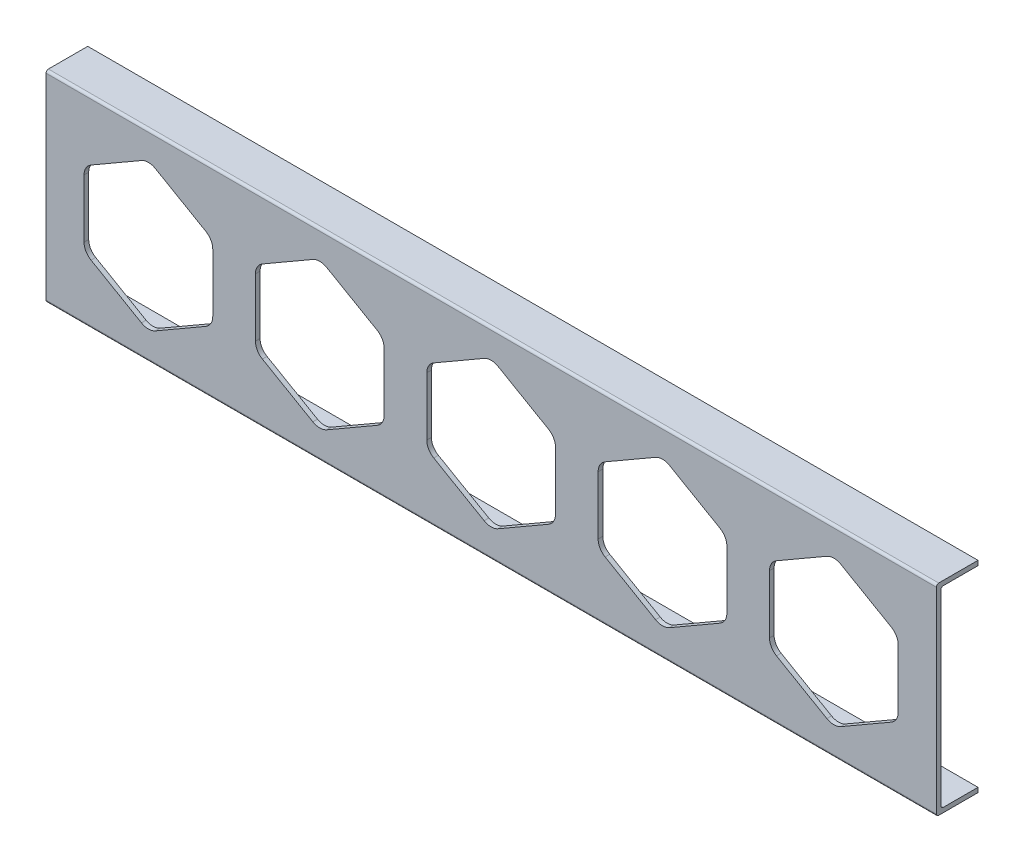
SolidWorks part; units mm, degrees
material "6061-T6 (SS)"
ref_plane "Front" through (0, 0, 0) normal (0, 0, 1) x (1, 0, 0)
ref_plane "Top" through (0, 0, 0) normal (0, 1, 0) x (1, 0, 0)
ref_plane "Right" through (0, 0, 0) normal (1, 0, 0) x (0, 0, -1)
sketch "Sketch1" plane through (0, 0, 0) normal (1, 0, 0) x (0, 0, -1)
  line L0 (-0.762, 67.2998) -> (12.7, 67.2998)
  line L1 (0.8255, 0) -> (12.7, 0)
  line L2 (0, 0.8255) -> (0, 64.8868)
  line L3 (0.8255, 65.7123) -> (12.7, 65.7123)
  line L5 (-1.5875, -0.762) -> (-1.5875, 66.4743)
  line L6 (-0.762, -1.5875) -> (12.7, -1.5875)
  line L7 (12.7, 65.7123) -> (12.7, 67.2998)
  line L8 (12.7, 0) -> (12.7, -1.5875)
  line L9 (-1.5875, -1.5875) -> (-1.5875, 67.2998) construction
  line L10 (-1.5875, -1.5875) -> (12.7, -1.5875) construction
  line L11 (0, 0) -> (12.7, 0) construction
  line L12 (0, 0) -> (0, 65.7123) construction
  line L13 (-1.5875, 67.2998) -> (12.7, 67.2998) construction
  line L14 (0, 65.7123) -> (12.7, 65.7123) construction
  arc A0 (-1.5875, -0.762) -> (-0.762, -1.5875) centre (-0.762, -0.762) ccw
  arc A1 (0.8255, 0) -> (0, 0.8255) centre (0.8255, 0.8255) cw
  arc A2 (-0.762, 67.2998) -> (-1.5875, 66.4743) centre (-0.762, 66.4743) ccw
  arc A3 (0, 64.8868) -> (0.8255, 65.7123) centre (0.8255, 64.8868) cw
  point P15 (0, 0)
  dimension "D4" = 0.8255
  dimension "D2" = 12.7
  dimension "D3" = 1.5875
extrude "Boss-Extrude1" add sketch "Sketch1" along normal blind 304.8
sketch "Sketch2" plane through (0, 0, 1.5875) normal (0, 0, 1) x (1, 0, 0)
  line L0 (35.0626, 32.8562) -> (35.0626, 66.4743) construction
  line L1 (32.6813, 56.9215) -> (15.412, 46.9511)
  line L2 (13.0307, 42.8266) -> (13.0307, 22.8857)
  line L3 (15.412, 18.7613) -> (32.6813, 8.7908)
  line L4 (37.4438, 8.7908) -> (54.7132, 18.7613)
  line L5 (57.0944, 22.8857) -> (57.0944, 42.8266)
  line L6 (54.7132, 46.9511) -> (37.4438, 56.9215)
  line L7 (304.8, 66.4743) -> (0, 66.4743) construction
  line L8 (35.0626, 32.8562) -> (35.0626, -0.762) construction
  line L9 (304.8, -0.762) -> (0, -0.762) construction
  line L10 (91.35, 56.9215) -> (74.0807, 46.9511)
  line L11 (71.6994, 42.8266) -> (71.6994, 22.8857)
  line L12 (74.0807, 18.7613) -> (91.35, 8.7908)
  line L13 (96.1125, 8.7908) -> (113.3819, 18.7613)
  line L14 (115.7631, 22.8857) -> (115.7631, 42.8266)
  line L15 (113.3819, 46.9511) -> (96.1125, 56.9215)
  line L16 (150.0188, 56.9215) -> (132.7494, 46.9511)
  line L17 (130.3681, 42.8266) -> (130.3681, 22.8857)
  line L18 (132.7494, 18.7613) -> (150.0188, 8.7908)
  line L19 (154.7812, 8.7908) -> (172.0506, 18.7613)
  line L20 (174.4319, 22.8857) -> (174.4319, 42.8266)
  line L21 (172.0506, 46.9511) -> (154.7812, 56.9215)
  line L22 (208.6875, 56.9215) -> (191.4181, 46.9511)
  line L23 (189.0369, 42.8266) -> (189.0369, 22.8857)
  line L24 (191.4181, 18.7613) -> (208.6875, 8.7908)
  line L25 (213.45, 8.7908) -> (230.7193, 18.7613)
  line L26 (233.1006, 22.8857) -> (233.1006, 42.8266)
  line L27 (230.7193, 46.9511) -> (213.45, 56.9215)
  line L28 (267.3562, 56.9215) -> (250.0868, 46.9511)
  line L29 (247.7056, 42.8266) -> (247.7056, 22.8857)
  line L30 (250.0868, 18.7613) -> (267.3562, 8.7908)
  line L31 (272.1187, 8.7908) -> (289.388, 18.7613)
  line L32 (291.7693, 22.8857) -> (291.7693, 42.8266)
  line L33 (289.388, 46.9511) -> (272.1187, 56.9215)
  line L34 (13.0307, 38.3584) -> (0, 38.3584) construction
  line L35 (0, 66.4743) -> (0, -0.762) construction
  line L36 (291.7693, 29.4986) -> (304.8, 29.4986) construction
  line L37 (304.8, 66.4743) -> (304.8, -0.762) construction
  arc A0 (57.0944, 42.8266) -> (54.7132, 46.9511) centre (52.3319, 42.8266) ccw
  arc A1 (54.7132, 18.7613) -> (57.0944, 22.8857) centre (52.3319, 22.8857) ccw
  arc A2 (32.6813, 8.7908) -> (37.4438, 8.7908) centre (35.0626, 12.9152) ccw
  arc A3 (13.0307, 22.8857) -> (15.412, 18.7613) centre (17.7932, 22.8857) ccw
  arc A4 (15.412, 46.9511) -> (13.0307, 42.8266) centre (17.7932, 42.8266) ccw
  arc A5 (32.6813, 56.9215) -> (37.4438, 56.9215) centre (35.0626, 52.7971) cw
  arc A6 (115.7631, 42.8266) -> (113.3819, 46.9511) centre (111.0006, 42.8266) ccw
  arc A7 (113.3819, 18.7613) -> (115.7631, 22.8857) centre (111.0006, 22.8857) ccw
  arc A8 (91.35, 8.7908) -> (96.1125, 8.7908) centre (93.7313, 12.9152) ccw
  arc A9 (71.6994, 22.8857) -> (74.0807, 18.7613) centre (76.4619, 22.8857) ccw
  arc A10 (74.0807, 46.9511) -> (71.6994, 42.8266) centre (76.4619, 42.8266) ccw
  arc A11 (91.35, 56.9215) -> (96.1125, 56.9215) centre (93.7313, 52.7971) cw
  arc A12 (174.4319, 42.8266) -> (172.0506, 46.9511) centre (169.6694, 42.8266) ccw
  arc A13 (172.0506, 18.7613) -> (174.4319, 22.8857) centre (169.6694, 22.8857) ccw
  arc A14 (150.0188, 8.7908) -> (154.7812, 8.7908) centre (152.4, 12.9152) ccw
  arc A15 (130.3681, 22.8857) -> (132.7494, 18.7613) centre (135.1306, 22.8857) ccw
  arc A16 (132.7494, 46.9511) -> (130.3681, 42.8266) centre (135.1306, 42.8266) ccw
  arc A17 (150.0188, 56.9215) -> (154.7812, 56.9215) centre (152.4, 52.7971) cw
  arc A18 (233.1006, 42.8266) -> (230.7193, 46.9511) centre (228.3381, 42.8266) ccw
  arc A19 (230.7193, 18.7613) -> (233.1006, 22.8857) centre (228.3381, 22.8857) ccw
  arc A20 (208.6875, 8.7908) -> (213.45, 8.7908) centre (211.0687, 12.9152) ccw
  arc A21 (189.0369, 22.8857) -> (191.4181, 18.7613) centre (193.7994, 22.8857) ccw
  arc A22 (191.4181, 46.9511) -> (189.0369, 42.8266) centre (193.7994, 42.8266) ccw
  arc A23 (208.6875, 56.9215) -> (213.45, 56.9215) centre (211.0687, 52.7971) cw
  arc A24 (291.7693, 42.8266) -> (289.388, 46.9511) centre (287.0068, 42.8266) ccw
  arc A25 (289.388, 18.7613) -> (291.7693, 22.8857) centre (287.0068, 22.8857) ccw
  arc A26 (267.3562, 8.7908) -> (272.1187, 8.7908) centre (269.7374, 12.9152) ccw
  arc A27 (247.7056, 22.8857) -> (250.0868, 18.7613) centre (252.4681, 22.8857) ccw
  arc A28 (250.0868, 46.9511) -> (247.7056, 42.8266) centre (252.4681, 42.8266) ccw
  arc A29 (267.3562, 56.9215) -> (272.1187, 56.9215) centre (269.7374, 52.7971) cw
  point P19 (35.0626, 7.416)
  point P26 (35.0626, 58.2964)
  dimension "D1" = 4.7625
  dimension "D3" = 14.605
  dimension "D4" = 19.9409
  dimension "D2" = 5
extrude "Cut-Extrude1" cut sketch "Sketch2" against normal up to next
